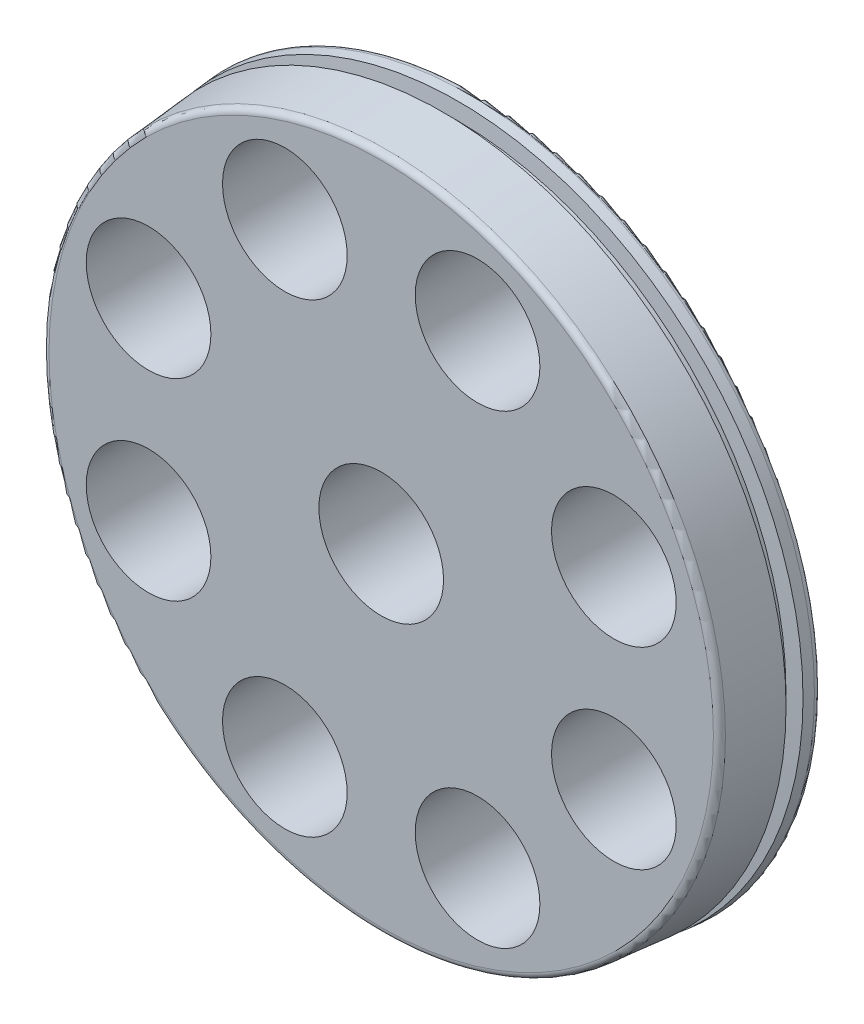
SolidWorks part; units mm, degrees
material "PE High Density"
ref_plane "Front Plane" through (0, 0, 0) normal (0, 0, 1) x (1, 0, 0)
ref_plane "Top Plane" through (0, 0, 0) normal (0, 1, 0) x (1, 0, 0)
ref_plane "Right Plane" through (0, 0, 0) normal (1, 0, 0) x (0, 0, -1)
sketch "Sketch1" plane through (0, 0, 0) normal (0, 0, 1) x (1, 0, 0)
  circle A3 centre (0, 0) radius 69.85
  dimension "D2" = 139.7
extrude "Boss-Extrude1" add sketch "Sketch1" along normal blind 19.05 draft 5
fillet "Fillet2" radius 1.27 2 edges at (69.85, 0, 0) (68.1833, 0, 19.05)
sketch "Sketch2" plane through (0, 0, 0) normal (0, 1, 0) x (1, 0, 0)
  line L0 (0, 0) -> (0, -19.05) construction
  line L1 (-67.0196, -19.05) -> (67.0196, -19.05) construction
  line L2 (-69.4056, -5.08) -> (69.4056, -5.08) construction
  line L3 (-69.7292, -1.3807) -> (-68.2848, -17.8907) construction
  line L4 (68.2848, -17.8907) -> (69.7292, -1.3807) construction
  line L5 (-66.3694, -3.7703) -> (-66.3694, -6.3897)
  line L6 (-66.3694, -6.3897) -> (-69.5444, -6.6675)
  line L7 (-69.5444, -6.6675) -> (-69.5444, -3.4925)
  line L8 (-69.5444, -3.4925) -> (-66.3694, -3.7703)
  point P13 (-66.3694, -5.08)
  point P16 (-69.5444, -5.08)
  dimension "D1" = 5.08
  dimension "D2" = 3.175
  dimension "D3" = 85
  dimension "D4" = 3.175
revolve "Cut-Revolve1" cut sketch "Sketch2" angle 360 about L0
sketch "Sketch3" plane through (0, 0, 0) normal (0, 0, -1) x (-1, 0, 0)
  line L0 (0, 0) -> (0, 50.8) construction
  line L1 (0, 0) -> (19.4403, 46.9331) construction
  circle A0 centre (0, 0) radius 1.905 construction
  circle A1 centre (19.4403, 46.9331) radius 1.905 construction
  circle A2 centre (0, 0) radius 50.8 construction
  circle A3 centre (46.9331, 19.4403) radius 1.905 construction
  circle A4 centre (46.9331, -19.4403) radius 1.905 construction
  circle A5 centre (19.4403, -46.9331) radius 1.905 construction
  circle A6 centre (-19.4403, -46.9331) radius 1.905 construction
  circle A7 centre (-46.9331, -19.4403) radius 1.905 construction
  circle A8 centre (-46.9331, 19.4403) radius 1.905 construction
  circle A9 centre (-19.4403, 46.9331) radius 1.905 construction
  circle A10 centre (-19.4403, 46.9331) radius 12.573
  circle A11 centre (19.4403, 46.9331) radius 12.573
  circle A12 centre (46.9331, 19.4403) radius 12.573
  circle A13 centre (46.9331, -19.4403) radius 12.573
  circle A14 centre (19.4403, -46.9331) radius 12.573
  circle A15 centre (-19.4403, -46.9331) radius 12.573
  circle A16 centre (-46.9331, -19.4403) radius 12.573
  circle A17 centre (-46.9331, 19.4403) radius 12.573
  circle A18 centre (0, 0) radius 12.573
  point P23 (0, 0)
  dimension "D1" = 3.81
  dimension "D2" = 50.8
  dimension "D3" = 22.5
  dimension "D5" = 10.668
  dimension "D6" = 10.668
  dimension "D4" = 8
extrude "Cut-Extrude1" cut sketch "Sketch3" against normal up to surface (19.05 mm away) up to face at (67.0196, 0, 19.05)
